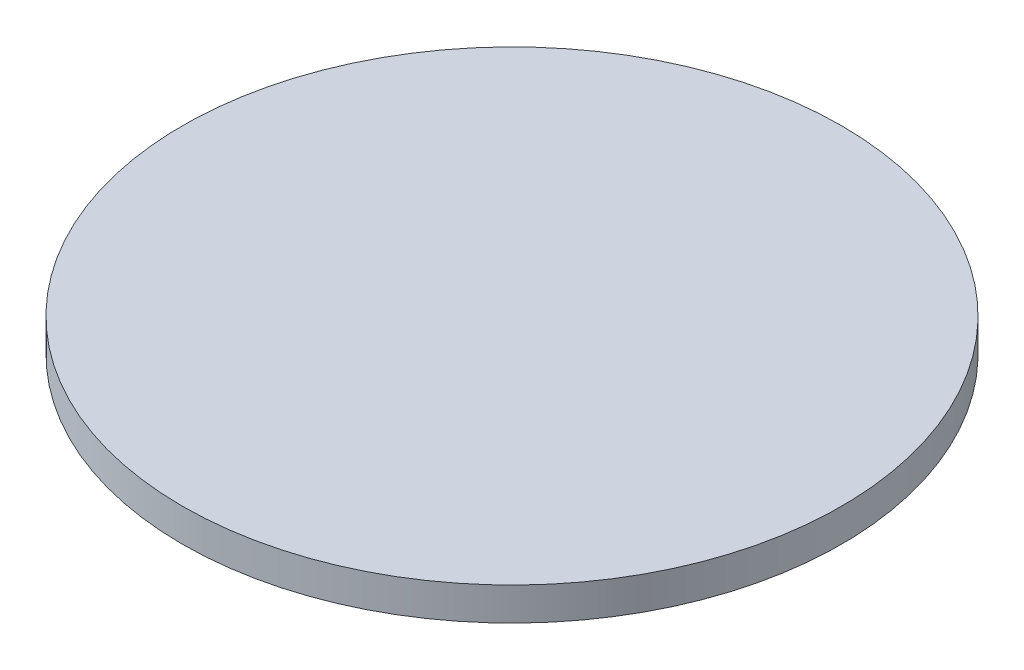
SolidWorks part; units mm, degrees
ref_plane "Front Plane" through (0, 0, 0) normal (0, 0, 1) x (1, 0, 0)
ref_plane "Top Plane" through (0, 0, 0) normal (0, 1, 0) x (1, 0, 0)
ref_plane "Right Plane" through (0, 0, 0) normal (1, 0, 0) x (0, 0, -1)
sketch "Sketch1" plane through (0, 0, 0) normal (0, 1, 0) x (1, 0, 0)
  circle A0 centre (0, 0) radius 50
extrude "Boss-Extrude1" add sketch "Sketch1" along normal blind 5
